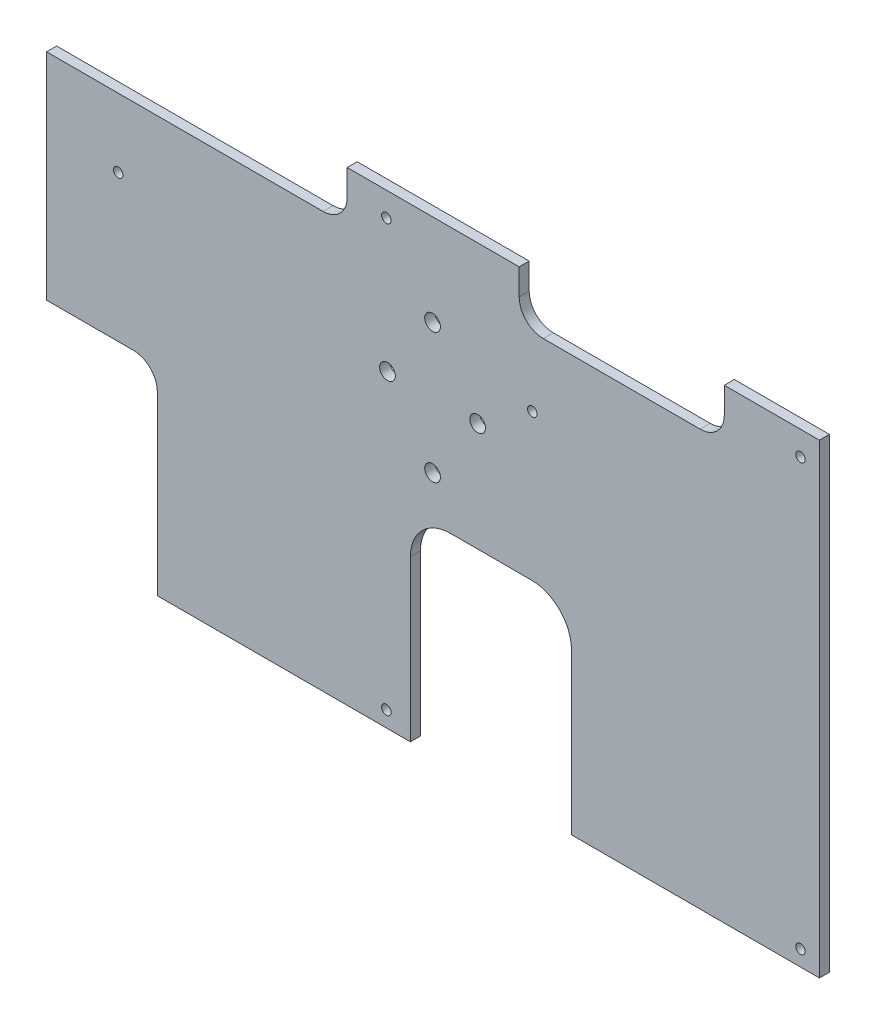
SolidWorks part; units mm, degrees
ref_plane "Front Plane" through (0, 0, 0) normal (0, 0, 1) x (1, 0, 0)
ref_plane "Top Plane" through (0, 0, 0) normal (0, 1, 0) x (1, 0, 0)
ref_plane "Right Plane" through (0, 0, 0) normal (1, 0, 0) x (0, 0, -1)
sketch "Model" plane through (0, 0, 0) normal (0, 0, 1) x (1, 0, 0)
  line L0 (218.0572, 213.425) -> (209.3472, 213.425) construction
  line L1 (218.0572, 162.555) -> (218.0572, 213.425) construction
  line L2 (339.5972, 162.555) -> (440.5972, 162.555) construction
  line L3 (349.3072, 162.555) -> (349.3072, 213.425) construction
  line L4 (349.3072, 226.125) -> (323.6672, 226.125)
  line L5 (362.0072, 162.555) -> (362.0072, 213.425)
  line L6 (440.5972, 162.555) -> (362.0072, 162.555)
  line L7 (440.5972, 310.175) -> (440.5972, 162.555)
  line L8 (195.6472, 310.175) -> (440.5972, 310.175)
  line L9 (195.6472, 226.125) -> (195.6472, 310.175)
  line L10 (223.1372, 226.125) -> (195.6472, 226.125)
  line L11 (230.7572, 162.555) -> (230.7572, 218.505)
  line L12 (310.9672, 162.555) -> (230.7572, 162.555)
  line L13 (310.9672, 213.425) -> (310.9672, 162.555)
  line L14 (349.3072, 213.425) -> (340.5972, 213.425) construction
  line L15 (440.5972, 162.555) -> (440.5972, 321.555) construction
  line L16 (208.3472, 321.555) -> (208.3472, 162.555) construction
  line L18 (195.6472, 294.3) -> (283.2938, 294.3)
  line L19 (195.6472, 294.3) -> (195.6472, 310.175)
  line L20 (195.6472, 310.175) -> (290.9138, 310.175)
  line L21 (290.9138, 301.92) -> (290.9138, 310.175)
  line L22 (345.4347, 310.175) -> (410.4342, 310.175)
  line L23 (345.4347, 310.175) -> (345.4347, 301.92)
  line L24 (353.0547, 294.3) -> (402.8142, 294.3)
  line L25 (410.4342, 310.175) -> (410.4342, 301.92)
  circle A0 centre (434.5972, 167.555) radius 1.5 construction
  circle A1 centre (317.9897, 281.2085) radius 2.4892 construction
  circle A2 centre (317.9897, 239.9335) radius 2.4892 construction
  circle A3 centre (349.5972, 272.555) radius 1.5 construction
  arc A4 (323.6672, 226.125) -> (310.9672, 213.425) centre (323.6672, 213.425) ccw
  arc A5 (362.0072, 213.425) -> (349.3072, 226.125) centre (349.3072, 213.425) ccw
  circle A6 centre (303.3472, 167.555) radius 1.5 construction
  circle A7 centre (317.9897, 239.9335) radius 2.4892
  circle A8 centre (303.7022, 260.571) radius 2.4892
  circle A9 centre (317.9897, 281.2085) radius 2.4892
  circle A10 centre (218.3472, 272.555) radius 1.5 construction
  circle A11 centre (218.3472, 272.555) radius 1.5
  circle A12 centre (303.3472, 302.555) radius 1.5
  circle A13 centre (303.3472, 167.555) radius 1.5
  circle A14 centre (332.2772, 260.571) radius 2.4892
  circle A15 centre (434.5972, 302.555) radius 1.5
  circle A16 centre (434.5972, 167.555) radius 1.5
  circle A17 centre (434.5972, 302.555) radius 1.5 construction
  circle A18 centre (349.5972, 272.555) radius 1.5
  circle A19 centre (303.3472, 302.555) radius 1.5 construction
  arc A20 (223.1372, 226.125) -> (230.7572, 218.505) centre (223.1372, 218.505) cw
  arc A21 (410.4342, 301.92) -> (402.8142, 294.3) centre (402.8142, 301.92) cw
  arc A22 (345.4347, 301.92) -> (353.0547, 294.3) centre (353.0547, 301.92) ccw
  arc A23 (290.9138, 301.92) -> (283.2938, 294.3) centre (283.2938, 301.92) cw
  circle A24 centre (332.2772, 260.571) radius 2.4892 construction
  circle A25 centre (303.7022, 260.571) radius 2.4892 construction
  dimension "D5" = 12.7
  dimension "D9" = 7.62
  dimension "D1" = 12.7
  dimension "D2" = 12.7
  dimension "D3" = 12.7
  dimension "D4" = 12.7
  dimension "D6" = 7.62
  dimension "D7" = 12.7
  dimension "D8" = 7.62
  dimension "D10" = 15.875
extrude "Boss-Extrude1" add sketch "Model" along normal blind 3.175 contours L21 A23 L18 L9 L10 A20 L11 L12 L13 A4 L4 A5 L5 L6 L7 L8 L25 A21 L24 A22 L23 A7 A8 A9 A11 A12 A13 A14 A15 A16 A18
